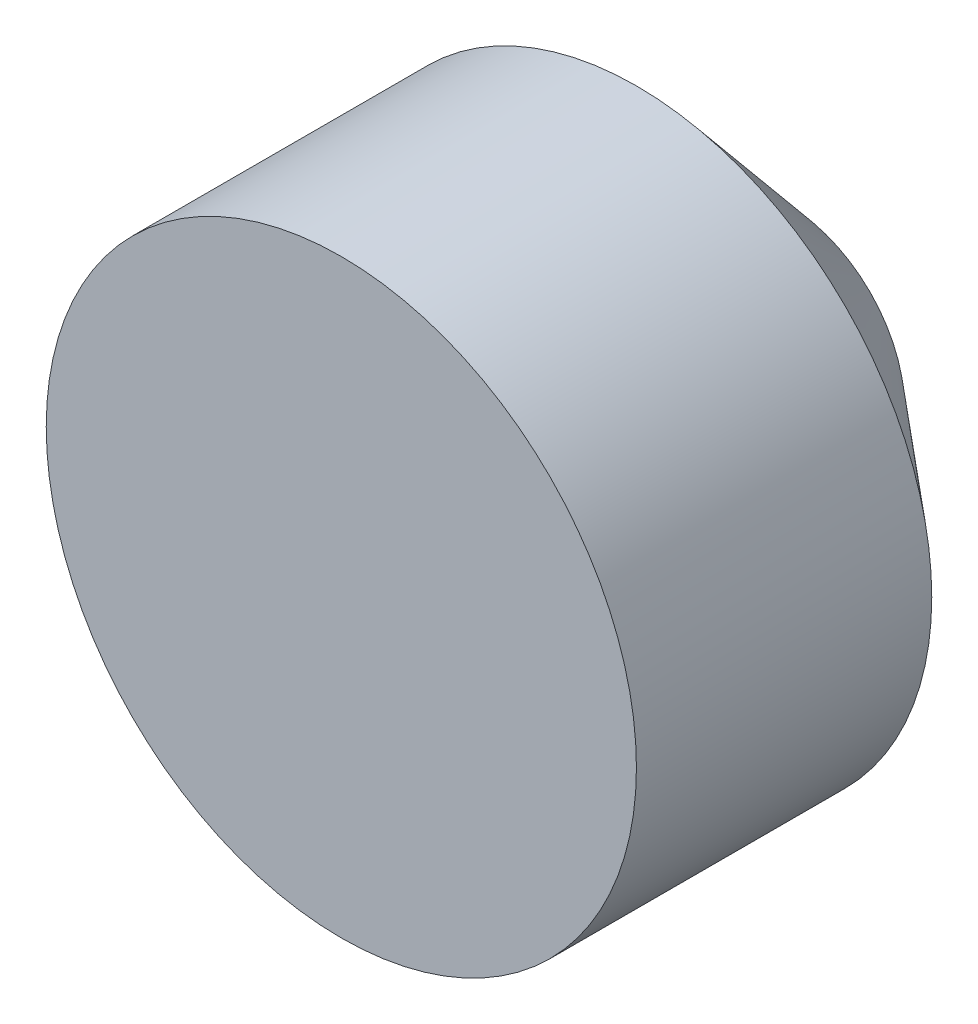
SolidWorks part; units mm, degrees
other "Markup1"
sketch "Sketch6" plane through (500, -500, -1363.6) normal (1, 0, 0) x (0, 0, -1)
ref_plane "Top Plane" through (0, 0, 0) normal (0, 0, 1) x (1, 0, 0)
ref_plane "Right Plane" through (0, 0, 0) normal (0, 1, 0) x (1, 0, 0)
ref_plane "Front Plane" through (0, 0, 0) normal (1, 0, 0) x (0, 0, -1)
sketch "Sketch5" plane through (0, 0, 0) normal (1, 0, 0) x (0, 0, -1)
  line L0 (0, 0) -> (0, 500)
  line L2 (0, 500) -> (500.38, 500)
  line L3 (500.38, 500) -> (754.38, 200)
  line L4 (754.38, 200) -> (754.38, 0)
  line L5 (754.38, 0) -> (0, 0)
  dimension "D1" = 500
  dimension "D2" = 500.38
  dimension "D3" = 754.38
  dimension "D4" = 200
revolve "Revolve1" add sketch "Sketch5" angle 360 about L5
